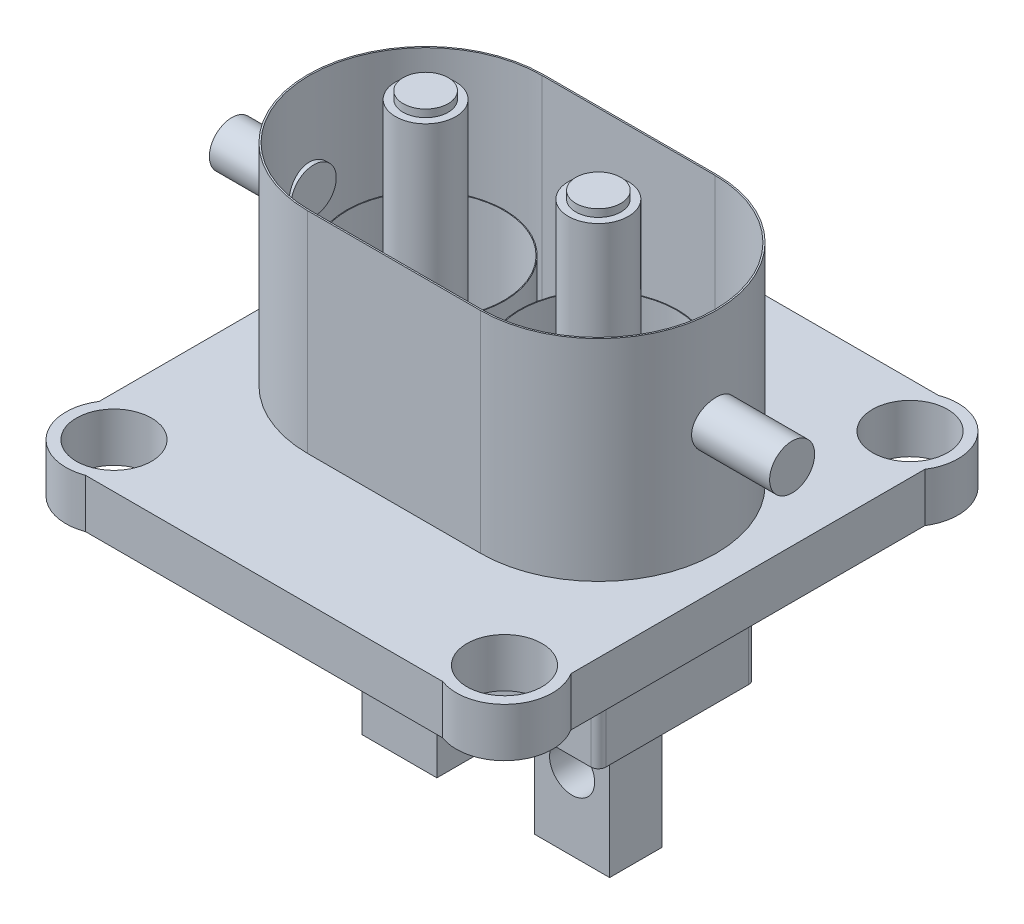
SolidWorks part; units mm, degrees
ref_plane "Płaszczyzna XY" through (0, 0, 0) normal (0, 0, 1) x (1, 0, 0)
ref_plane "Płaszczyzna XZ" through (0, 0, 0) normal (0, 1, 0) x (1, 0, 0)
ref_plane "Płaszczyzna YZ" through (0, 0, 0) normal (1, 0, 0) x (0, 0, -1)
sketch "Szkic1" plane through (0, 0, 0) normal (0, 1, 0) x (1, 0, 0)
  line L0 (-49.9204, 35.3191) -> (-49.9204, -21.8809)
  line L1 (-45.5204, 39.7191) -> (8.4796, 39.7191)
  line L2 (12.8796, 35.3191) -> (12.8796, -21.8809)
  line L3 (8.4796, -26.2809) -> (-45.5204, -26.2809)
  arc A0 (8.4796, 39.7191) -> (12.8796, 35.3191) centre (8.4796, 35.3191) cw
  arc A1 (-49.9204, 35.3191) -> (-45.5204, 39.7191) centre (-45.5204, 35.3191) cw
  arc A2 (-49.9204, -21.8809) -> (-45.5204, -26.2809) centre (-45.5204, -21.8809) ccw
  arc A3 (12.8796, -21.8809) -> (8.4796, -26.2809) centre (8.4796, -21.8809) cw
  dimension "D1" = 4.4
  dimension "D2" = 4.4
  dimension "D3" = 4.4
  dimension "D4" = 4.4
extrude "Dodanie-wyciągnięcie1" add sketch "Szkic1" along normal blind 6.5 contours L0 A2 L3 A3 L2 A0 L1 A1
sketch "Szkic2" plane through (0, 0, 0) normal (0, 1, 0) x (1, 0, 0)
  line L8 (-18.5204, 39.7191) -> (-18.5204, -20.0608) construction
  line L10 (-49.9204, 6.7191) -> (3.9083, 6.7191) construction
  line L17 (12.8796, 35.3191) -> (12.8796, -21.8809) construction
  line L18 (8.4796, -26.2809) -> (-45.5204, -26.2809) construction
  circle A0 centre (-44.5204, 33.7191) radius 6.4
  circle A4 centre (-44.5204, -20.2809) radius 6.4
  circle A5 centre (7.4796, -20.2809) radius 6.4
  circle A6 centre (7.4796, 33.7191) radius 6.4
  dimension "D1" = 52
  dimension "D2" = 12.8
  dimension "D4" = 5.4
  dimension "D3" = 54
  dimension "D5" = 6
extrude "Dodanie-wyciągnięcie2" add sketch "Szkic2" along normal blind 6.5 contours A0 | A4 | A5 | A6
sketch "Szkic3" plane through (0, 6.5, 0) normal (0, 1, 0) x (1, 0, 0)
  line L0 (-18.5204, 39.7191) -> (-18.5204, -1.0412) construction
  line L2 (-49.9204, 6.7191) -> (10.9061, 6.7191) construction
  circle A0 centre (7.4796, 33.7191) radius 5
  circle A1 centre (-44.5204, 33.7191) radius 5
  circle A2 centre (7.4796, -20.2809) radius 5
  circle A3 centre (-44.5204, -20.2809) radius 5
  dimension "D1" = 10
  dimension "D2" = 52
  dimension "D3" = 54
extrude "Wytnij-wyciągnięcie4" cut sketch "Szkic3" against normal blind 6.5
sketch "Szkic4" plane through (0, 6.5, 0) normal (0, 1, 0) x (1, 0, 0)
  line L1 (-49.9204, 30.284) -> (-49.9204, -16.8457) construction
  line L5 (-49.9204, 6.7191) -> (16.3477, 6.7191) construction
  line L6 (-18.5204, 39.7191) -> (-18.5204, 6.7191) construction
  line L9 (-42.2933, 39.7191) -> (5.2525, 39.7191) construction
  circle A11 centre (-30.0204, 6.7191) radius 10.5
  circle A12 centre (-30.0204, 6.7191) radius 10.4
  circle A13 centre (-7.0204, 6.7191) radius 10.4
  circle A14 centre (-7.0204, 6.7191) radius 10.5
  dimension "D2" = 33
  dimension "D5" = 20.8
  dimension "D3" = 21
  dimension "D1" = 31.4
  dimension "D6" = 19.9
extrude "Dodanie-wyciągnięcie3" add sketch "Szkic4" along normal blind 15
sketch "Szkic5" plane through (0, 0, 0) normal (0, -1, 0) x (-1, 0, 0)
  line L0 (18.5204, 39.7191) -> (18.5204, -30.5553) construction
  line L1 (42.2933, 39.7191) -> (-5.2525, 39.7191) construction
  line L2 (-19.8064, 6.7191) -> (42.3757, 6.7191) construction
  line L3 (-12.8796, 30.284) -> (-12.8796, -16.8457) construction
  line L4 (-3.4796, -2.7809) -> (-3.4796, 16.2191)
  line L5 (-2.4796, 17.2191) -> (39.5204, 17.2191)
  line L6 (40.5204, -2.7809) -> (40.5204, 16.2191)
  line L7 (-2.4796, -3.7809) -> (39.5204, -3.7809)
  arc A0 (-3.4796, 16.2191) -> (-2.4796, 17.2191) centre (-2.4796, 16.2191) cw
  arc A1 (40.5204, 16.2191) -> (39.5204, 17.2191) centre (39.5204, 16.2191) ccw
  arc A2 (40.5204, -2.7809) -> (39.5204, -3.7809) centre (39.5204, -2.7809) cw
  arc A3 (-3.4796, -2.7809) -> (-2.4796, -3.7809) centre (-2.4796, -2.7809) ccw
  point P13 (18.5204, 17.2191)
  point P14 (40.5204, 6.7191)
  point P19 (-3.4796, 6.7191)
  point P21 (18.5204, 39.7191)
  point P24 (-12.8796, 6.7191)
  dimension "D1" = 1
  dimension "D2" = 22
  dimension "D3" = 10.5
extrude "Dodanie-wyciągnięcie4" add sketch "Szkic5" along normal blind 16
sketch "Szkic6" plane through (0, 0, 0) normal (0, -1, 0) x (-1, 0, 0)
  line L0 (18.5204, -26.2809) -> (18.5204, 36.0937) construction
  line L2 (51.5206, 6.7191) -> (-7.1201, 6.7191) construction
  line L4 (35.0204, 10.2191) -> (35.0204, 3.2191)
  line L5 (35.0204, 3.2191) -> (25.0204, 3.2191)
  line L6 (25.0204, 3.2191) -> (25.0204, 10.2191)
  line L7 (35.0204, 10.2191) -> (25.0204, 10.2191)
  line L8 (2.0204, 10.2191) -> (12.0204, 10.2191)
  line L9 (2.0204, 10.2191) -> (2.0204, 3.2191)
  line L10 (12.0204, 3.2191) -> (12.0204, 10.2191)
  line L11 (2.0204, 3.2191) -> (12.0204, 3.2191)
  line L12 (-5.2525, -26.2809) -> (42.2933, -26.2809) construction
  line L13 (49.9204, 30.284) -> (49.9204, -16.8457) construction
  point P9 (25.0204, 6.7191)
  point P10 (35.0204, 6.7191)
  point P16 (18.5204, -26.2809)
  point P19 (49.9204, 6.7191)
  dimension "D1" = 10
  dimension "D2" = 7
  dimension "D3" = 13
extrude "Dodanie-wyciągnięcie5" add sketch "Szkic6" along normal blind 34.5
sketch "Szkic7" plane through (0, 6.5, 0) normal (0, 1, 0) x (1, 0, 0)
  line L0 (-18.5204, 39.7191) -> (-18.5204, -28.1036) construction
  line L1 (-42.2933, 39.7191) -> (5.2525, 39.7191) construction
  circle A0 centre (-30.0204, 6.7191) radius 4
  circle A1 centre (-7.0204, 6.7191) radius 4
  dimension "D1" = 8
extrude "Dodanie-wyciągnięcie6" add sketch "Szkic7" along normal blind 33 contours A0 | A1
sketch "Szkic8" plane through (0, 39.5, 0) normal (0, 1, 0) x (1, 0, 0)
  line L0 (-18.5204, 39.7191) -> (-18.5204, -49960.2809) construction
  line L1 (-42.2933, 39.7191) -> (5.2525, 39.7191) construction
  circle A0 centre (-30.0204, 6.7191) radius 3
  circle A1 centre (-7.0204, 6.7191) radius 3
  point P7 (-18.5204, 39.7191)
  dimension "D1" = 6
extrude "Dodanie-wyciągnięcie7" add sketch "Szkic8" along normal blind 1
sketch "Szkic9" plane through (-49.9204, 0, 0) normal (-1, 0, 0) x (0, 0, 1)
  line L0 (3.7809, 21.5) -> (-17.2191, 21.5) construction
  circle A0 centre (-6.7191, 21.5) radius 3
  dimension "D1" = 6
extrude "Dodanie-wyciągnięcie8" add sketch "Szkic9" along normal blind 5.9 and the other way blind 5 separate body
sketch "Szkic10" plane through (12.8796, 0, 0) normal (1, 0, 0) x (0, 0, -1)
  line L0 (17.2191, 21.5) -> (-3.7809, 21.5) construction
  circle A0 centre (6.7191, 21.5) radius 3
  dimension "D1" = 6
extrude "Dodanie-wyciągnięcie9" add sketch "Szkic10" along normal blind 5.9 and the other way blind 5 separate body contours A0
sketch "Szkic11" plane through (0, 6.5, 0) normal (0, 1, 0) x (1, 0, 0)
  line L0 (-18.5204, -26.2809) -> (-18.5204, 41.0879) construction
  line L1 (18.7796, 6.7191) -> (-58.9499, 6.7191) construction
  line L2 (12.8796, 30.284) -> (12.8796, -16.8457) construction
  line L3 (-7.0204, 22.4191) -> (-30.0204, 22.4191)
  line L4 (-7.0204, 22.2191) -> (-30.0204, 22.2191)
  line L5 (-7.0204, -8.7809) -> (-30.0204, -8.7809)
  line L6 (-7.0204, -8.9809) -> (-30.0204, -8.9809)
  line L8 (-42.2933, 39.7191) -> (5.2525, 39.7191) construction
  arc A0 (-7.0204, 22.4191) -> (-7.0204, -8.9809) centre (-7.0204, 6.7191) cw
  arc A1 (-7.0204, 22.2191) -> (-7.0204, -8.7809) centre (-7.0204, 6.7191) cw
  arc A2 (-30.0204, 22.4191) -> (-30.0204, -8.9809) centre (-30.0204, 6.7191) ccw
  arc A3 (-30.0204, 22.2191) -> (-30.0204, -8.7809) centre (-30.0204, 6.7191) ccw
  point P11 (-18.5204, 22.4191)
  point P12 (-18.5204, 22.2191)
  dimension "D1" = 15.5
  dimension "D2" = 15.7
  dimension "D3" = 31.4
  dimension "D4" = 17.3
  dimension "D5" = 17.5
extrude "Dodanie-wyciągnięcie10" add sketch "Szkic11" along normal blind 28 contours A0 L6 A2 L3 | A1 L5 A3 L4
sketch "Szkic12" plane through (0, 0, -3.2191) normal (0, 0, 1) x (1, 0, 0)
  line L0 (-7.0204, -37.1557) -> (-7.0204, 28.6363) construction
  line L3 (5.2525, 0) -> (-42.2933, 0) construction
  line L6 (-18.5204, -16) -> (-18.5204, 38.289) construction
  line L8 (13.8796, 0) -> (13.8796, 6.5) construction
  circle A0 centre (-7.0204, -24.5) radius 3
  circle A1 centre (-30.0204, -24.5) radius 3
  dimension "D1" = 6
  dimension "D2" = 24.5
  dimension "D3" = 11.5
  dimension "D4" = 32.4
extrude "Wytnij-wyciągnięcie5" cut sketch "Szkic12" against normal blind 7
